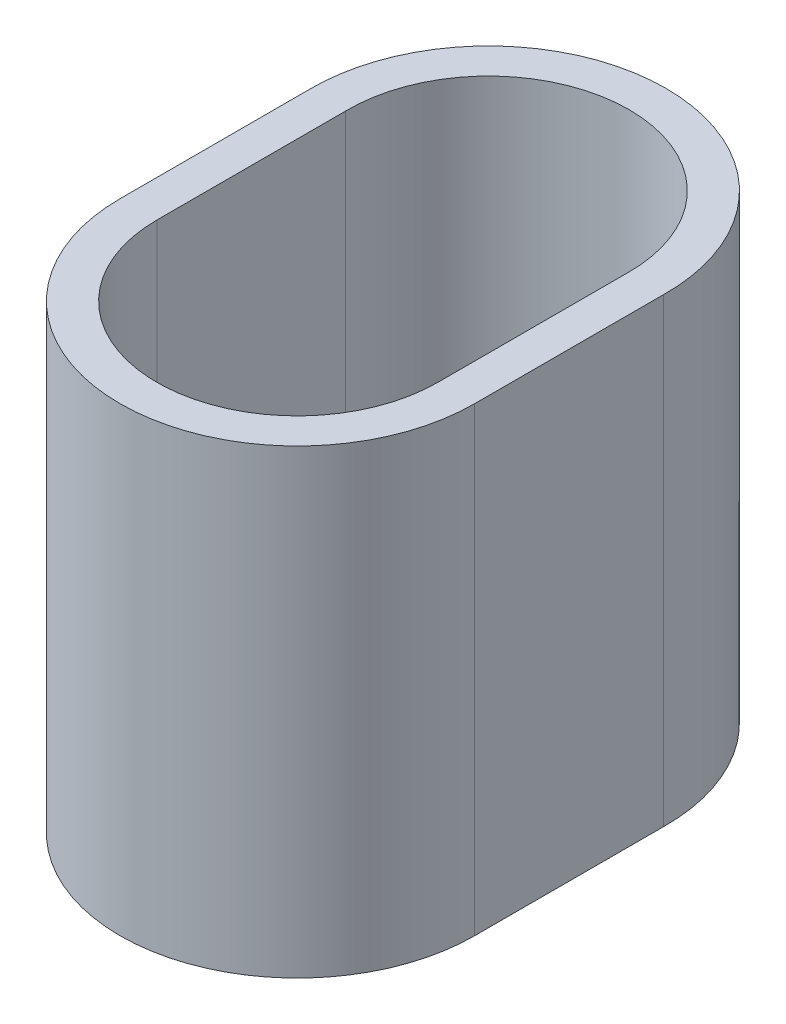
SolidWorks part; units mm, degrees
ref_plane "Front Plane" through (0, 0, 0) normal (0, 0, 1) x (1, 0, 0)
ref_plane "Top Plane" through (0, 0, 0) normal (0, 1, 0) x (1, 0, 0)
ref_plane "Right Plane" through (0, 0, 0) normal (1, 0, 0) x (0, 0, -1)
sketch "Sketch1" plane through (0, 0, 0) normal (0, 1, 0) x (1, 0, 0)
  line L0 (-20.0022, -10) -> (-20.0022, 10.4691)
  line L2 (-16.0022, -10) -> (-16.0022, 10.5)
  line L4 (14.4978, -10) -> (14.4978, 10.5)
  line L5 (18.4978, -10) -> (18.4978, 10.4691)
  arc A1 (-16.0022, -10) -> (14.4978, -10) centre (-0.7522, -10) ccw
  arc A2 (18.4978, 10.4691) -> (-20.0022, 10.4691) centre (-0.7522, 10.75) ccw
  arc A3 (14.4978, 10.5) -> (-16.0022, 10.5) centre (-0.7522, 10.75) ccw
  arc A4 (-20.0022, -10) -> (18.4978, -10) centre (-0.7522, -10) ccw
  point P0 (0, 0)
  dimension "D1" = 4
  dimension "D2" = 20.5
  dimension "D3" = 30.5
  dimension "D4" = 20.5
extrude "Boss-Extrude2" add sketch "Sketch1" along normal blind 50
